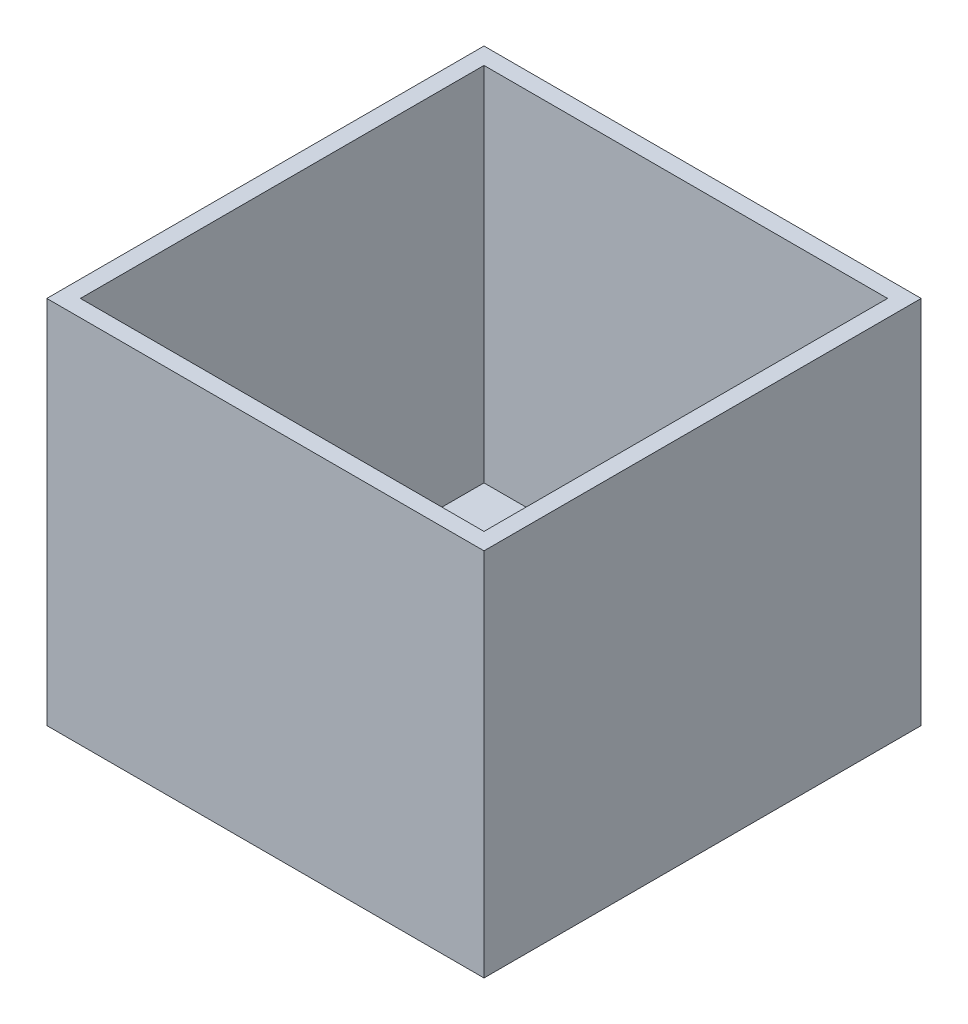
SolidWorks part; units mm, degrees
ref_plane "Front Plane" through (0, 0, 0) normal (0, 0, 1) x (1, 0, 0)
ref_plane "Top Plane" through (0, 0, 0) normal (0, 1, 0) x (1, 0, 0)
ref_plane "Right Plane" through (0, 0, 0) normal (1, 0, 0) x (0, 0, -1)
sketch "Sketch1" plane through (0, 0, 0) normal (0, 1, 0) x (1, 0, 0)
  line L1 (-165.1, -165.1) -> (165.1, -165.1)
  line L2 (-165.1, -165.1) -> (-165.1, 165.1)
  line L3 (-165.1, 165.1) -> (165.1, 165.1)
  line L4 (165.1, -165.1) -> (165.1, 165.1)
  line L5 (-165.1, -165.1) -> (165.1, 165.1) construction
  line L6 (-165.1, 165.1) -> (165.1, -165.1) construction
  point P0 (0, 0)
  dimension "D1" = 330.2
extrude "Boss-Extrude1" add sketch "Sketch1" along normal blind 279.4
sketch "Sketch2" plane through (0, 279.4, 0) normal (0, 1, 0) x (1, 0, 0)
  line L1 (-152.4, -152.4) -> (152.4, -152.4)
  line L2 (-152.4, -152.4) -> (-152.4, 152.4)
  line L3 (-152.4, 152.4) -> (152.4, 152.4)
  line L4 (152.4, -152.4) -> (152.4, 152.4)
  line L5 (-152.4, -152.4) -> (152.4, 152.4) construction
  line L6 (-152.4, 152.4) -> (152.4, -152.4) construction
  point P0 (0, 0)
  dimension "D1" = 304.8
extrude "Cut-Extrude1" cut sketch "Sketch2" against normal blind 273.05
